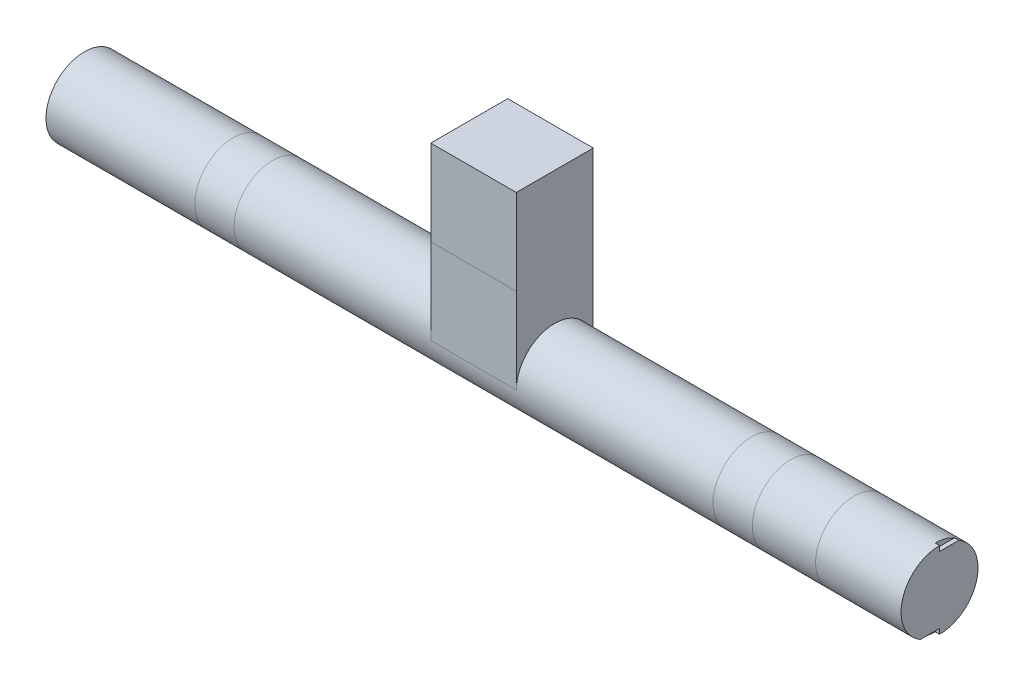
SolidWorks part; units mm, degrees
material "1.0037 (S235JR)"
ref_plane "Plan de face" through (0, 0, 0) normal (0, 0, 1) x (1, 0, 0)
ref_plane "Plan de dessus" through (0, 0, 0) normal (0, 1, 0) x (1, 0, 0)
ref_plane "Plan de droite" through (0, 0, 0) normal (1, 0, 0) x (0, 0, -1)
sketch "Esquisse1" plane through (0, 0, 0) normal (1, 0, 0) x (0, 0, -1)
  circle A0 centre (0, 0) radius 45
  dimension "D1" = 90
extrude "Boss.-Extru.1" add sketch "Esquisse1" along normal mid plane 1000
sketch "Esquisse2" plane through (0, 0, 0) normal (1, 0, 0) x (0, 0, -1)
  line L4 (-45, 200) -> (45, 200)
  line L5 (-45, 200) -> (-45, 0)
  line L6 (-45, 0) -> (45, 0)
  line L7 (45, 200) -> (45, 0)
  circle A2 centre (0, 0) radius 45 construction
  dimension "D1" = 200
extrude "Boss.-Extru.2" add sketch "Esquisse2" along normal mid plane 100
sketch "Esquisse3" plane through (0, 0, 0) normal (0, 0, 1) x (1, 0, 0)
  line L0 (-326, 45) -> (-326, -45)
  line L1 (-50, 45) -> (-500, 45) construction
  line L2 (-500, -45) -> (500, -45) construction
  line L4 (-280, 45) -> (-280, -45)
  line L5 (400, 45) -> (400, -45)
  line L6 (500, 45) -> (50, 45) construction
  line L7 (280, 45) -> (280, -45)
  line L8 (500, -45) -> (500, 45) construction
  line L9 (326, 45) -> (326, -45)
  dimension "D1" = 280
  dimension "D2" = 280
  dimension "D3" = 46
  dimension "D4" = 46
  dimension "D5" = 100
split line "Ligne de séparation1"
sketch "Esquisse5" plane through (0, 0, 0) normal (0, 0, 1) x (1, 0, 0)
  line L0 (-50, 100) -> (50, 100)
  line L1 (-50, 200) -> (-50, 0) construction
  line L2 (50, 200) -> (50, 0) construction
  line L3 (0, 200) -> (0, 100) construction
  line L4 (50, 200) -> (-50, 200) construction
  point P10 (0, 150)
  dimension "D1" = 150
split line "Ligne de séparation2"
sketch "Esquisse7" plane through (500, 0, 0) normal (1, 0, 0) x (0, 0, -1)
  line L0 (-73.1003, 0) -> (84.9401, 0) construction
  line L1 (22.4499, 39) -> (0, 39)
  line L2 (22.4499, 39) -> (22.4499, 45)
  line L3 (22.4499, 45) -> (0, 45)
  line L4 (0, 39) -> (0, 45)
  line L5 (-22.4499, -39) -> (0, -39)
  line L6 (-22.4499, -39) -> (-22.4499, -45)
  line L7 (-22.4499, -45) -> (0, -45)
  line L8 (0, -39) -> (0, -45)
  line L9 (0, -56.1783) -> (0, 61.769) construction
  circle A0 centre (0, 0) radius 45 construction
  point P15 (45, 0)
  point P17 (-45, 0)
  dimension "D1" = 6
extrude "Enlèv. mat.-Extru.1" cut sketch "Esquisse7" against normal blind 5
